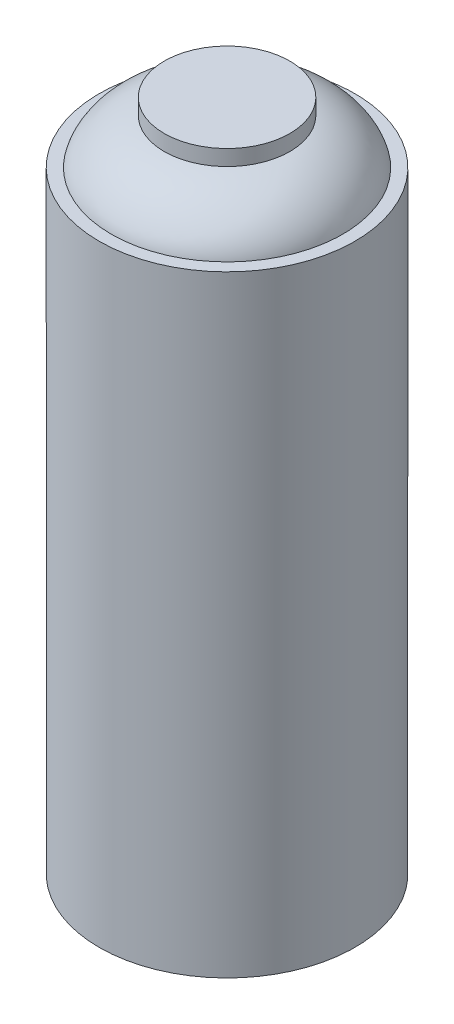
SolidWorks part; units mm, degrees
material "Custom Plastic"
ref_plane "Front Plane" through (0, 0, 0) normal (0, 0, 1) x (1, 0, 0)
ref_plane "Top Plane" through (0, 0, 0) normal (0, 1, 0) x (1, 0, 0)
ref_plane "Right Plane" through (0, 0, 0) normal (1, 0, 0) x (0, 0, -1)
sketch "Sketch1" plane through (0, 0, 0) normal (0, 0, 1) x (1, 0, 0)
  line L0 (0, 102.2904) -> (0, -64.2269)
  line L1 (33.04, -71.4096) -> (33.04, 86.5904)
  line L2 (33.04, 86.5904) -> (29.9, 86.5904)
  line L3 (16.225, 98.2504) -> (16.225, 102.2904)
  line L4 (16.225, 102.2904) -> (0, 102.2904)
  arc A0 (0, -64.2269) -> (33.04, -71.4096) centre (0, -143.8096) cw
  spline S0 degree 3 poles (29.9, 86.5904) (28.948, 91.0519) (23.9312, 96.6173) (16.225, 98.2504) knots 0 0 0 0 1 1 1 1
  dimension "D7" = 79.5827
  dimension "D1" = 33.04
  dimension "D2" = 158
  dimension "D3" = 15.7
  dimension "D4" = 3.14
  dimension "D5" = 16.225
  dimension "D6" = 4.04
  dimension "D8" = 26.7242
  dimension "D9" = 86.5904
  dimension "D10" = 92.3429
revolve "Revolve1" add sketch "Sketch1" angle 360 about L0
